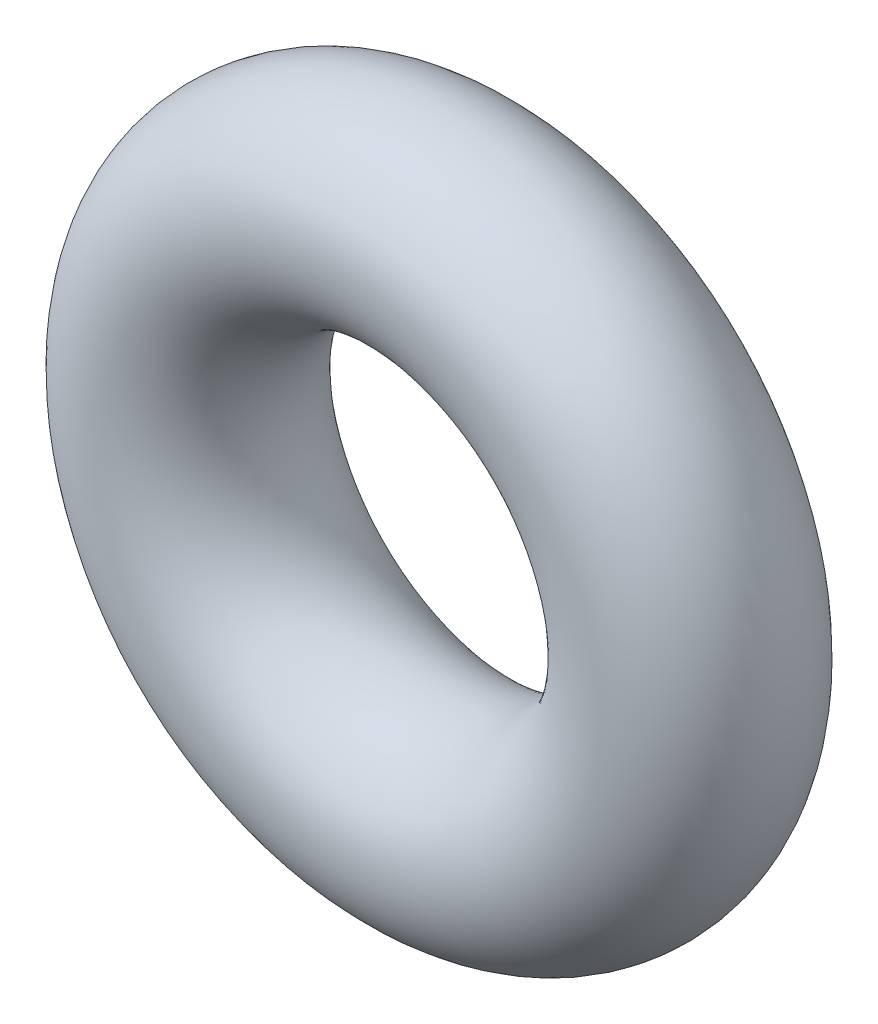
SolidWorks part; units mm, degrees
ref_plane "Front" through (0, 0, 0) normal (0, 0, 1) x (1, 0, 0)
ref_plane "Top" through (0, 0, 0) normal (0, 1, 0) x (1, 0, 0)
ref_plane "Right" through (0, 0, 0) normal (1, 0, 0) x (0, 0, -1)
sketch "Sketch1" plane through (0, 0, 0) normal (1, 0, 0) x (0, -1, 0)
  line L0 (0, -1) -> (0, 1) construction
  line L2 (-3.85, 0) -> (3.85, 0) construction
  line L3 (-1.5, 0) -> (1.5, 0) construction
  circle A0 centre (2.5, 0) radius 1
  point P9 (1.5, 0)
  point P10 (3.5, 0)
  point P13 (2.5, 1)
  point P14 (2.5, -1)
  dimension "Width" = 2
  dimension "ID" = 3
revolve "Revolve1" add sketch "Sketch1" angle 360 about L0
